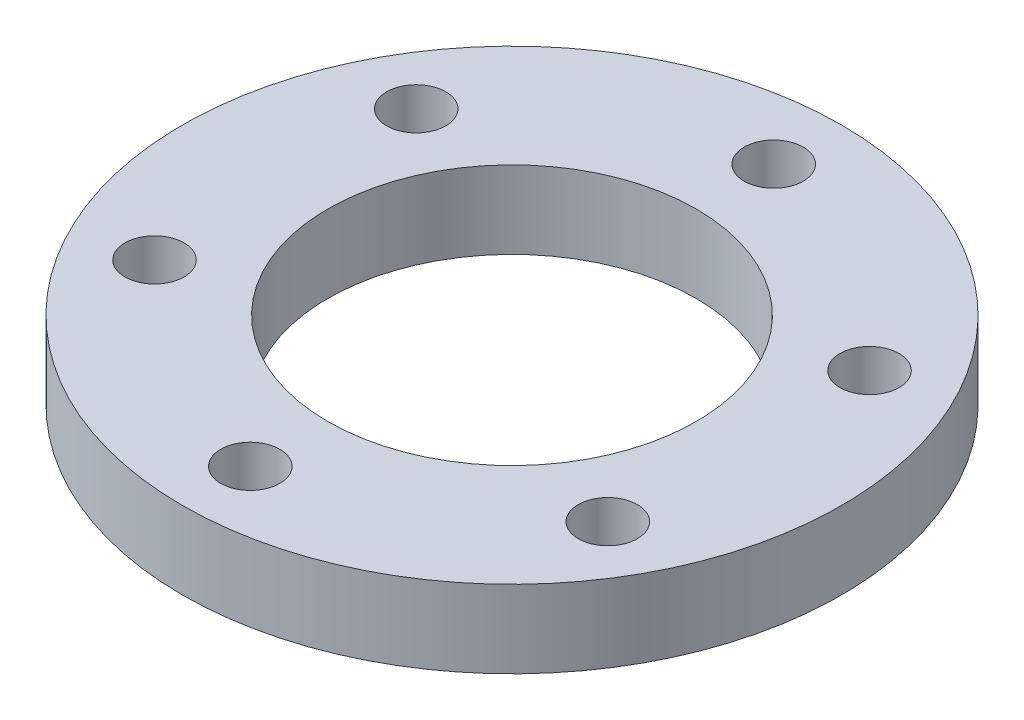
SolidWorks part; units mm, degrees
material "Thornel Mat VMA"
ref_plane "前视基准面" through (0, 0, 0) normal (0, 0, 1) x (1, 0, 0)
ref_plane "上视基准面" through (0, 0, 0) normal (0, 1, 0) x (1, 0, 0)
ref_plane "右视基准面" through (0, 0, 0) normal (1, 0, 0) x (0, 0, -1)
other "Configuration Table"
sketch "草图1" plane through (0, 0, 0) normal (0, 1, 0) x (1, 0, 0)
  circle A0 centre (0, 0) radius 17
  circle A1 centre (0, 0) radius 9.5
  dimension "D1" = 19
  dimension "D2" = 34
extrude "凸台-拉伸1" add sketch "草图1" along normal blind 4
sketch "草图2" plane through (0, 4, 0) normal (0, 1, 0) x (1, 0, 0)
  circle A0 centre (0, 0) radius 13.5 construction
  circle A1 centre (0, 13.5) radius 1.525
  circle A2 centre (11.6913, 6.75) radius 1.525
  circle A3 centre (11.6913, -6.75) radius 1.525
  circle A4 centre (0, -13.5) radius 1.525
  circle A5 centre (-11.6913, -6.75) radius 1.525
  circle A6 centre (-11.6913, 6.75) radius 1.525
  point P17 (0, 0)
  dimension "D1" = 27
  dimension "D2" = 3.05
extrude "切除-拉伸1" cut sketch "草图2" against normal blind 100
